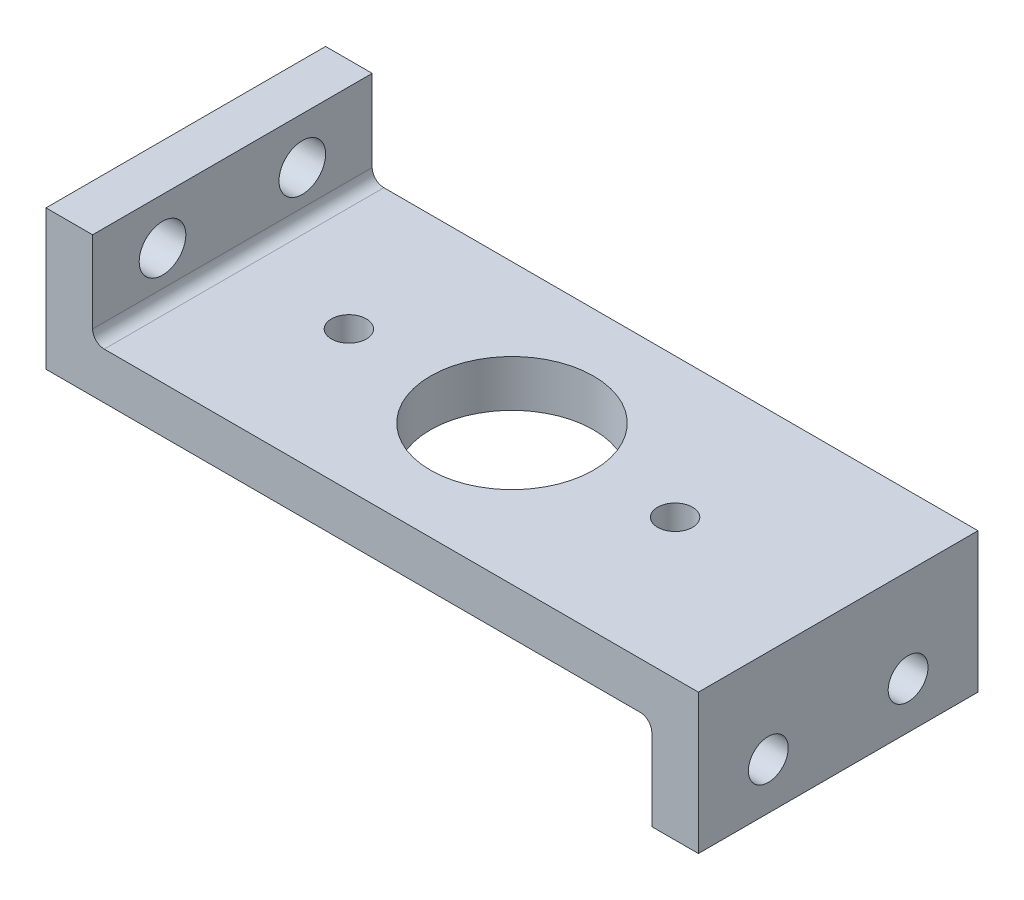
SolidWorks part; units mm, degrees
material "Alloy Steel"
ref_plane "Front Plane" through (0, 0, 0) normal (0, 0, 1) x (1, 0, 0)
ref_plane "Top Plane" through (0, 0, 0) normal (0, 1, 0) x (1, 0, 0)
ref_plane "Right Plane" through (0, 0, 0) normal (1, 0, 0) x (0, 0, -1)
sketch "Sketch1" plane through (0, 0, 0) normal (0, 0, 1) x (1, 0, 0)
  line L1 (-88.9, -4.8927) -> (73.025, -4.8927)
  line L2 (-88.9, -4.8927) -> (-88.9, 4.8927)
  line L3 (-73.025, 7.8073) -> (88.9, 7.8073)
  line L4 (88.9, -4.8927) -> (88.9, 7.8073)
  line L8 (-88.9, 4.8927) -> (-88.9, 33.2073)
  line L9 (-88.9, 33.2073) -> (-76.2, 33.2073)
  line L10 (-76.2, 10.9823) -> (-76.2, 33.2073)
  line L12 (88.9, -4.8927) -> (88.9, -30.2927)
  line L13 (88.9, -30.2927) -> (76.2, -30.2927)
  line L14 (76.2, -8.0677) -> (76.2, -30.2927)
  arc A0 (76.2, -8.0677) -> (73.025, -4.8927) centre (73.025, -8.0677) ccw
  arc A1 (-73.025, 7.8073) -> (-76.2, 10.9823) centre (-73.025, 10.9823) cw
  point P0 (0, 0)
  dimension "D7" = 3.175
  dimension "D1" = 12.7
  dimension "D2" = 12.7
  dimension "D3" = 38.1
  dimension "D4" = 38.1
  dimension "D5" = 177.8
  dimension "D6" = 12.7
extrude "Boss-Extrude1" add sketch "Sketch1" along normal blind 76.2
sketch "Sketch2" plane through (0, 0, 0) normal (0, 1, 0) x (1, 0, 0)
  line L0 (88.9, -76.2) -> (88.9, 0) construction
  line L1 (-34.925, 0) -> (34.925, 0) construction
  line L2 (-108.2905, -38.1) -> (131.2203, -38.1) construction
  line L3 (0, -38.1) -> (0, 39.7458) construction
  line L4 (88.9, -76.2) -> (-73.025, -76.2) construction
  circle A0 centre (0, -38.1) radius 22.225
  circle A1 centre (-44.45, -38.1) radius 4.7625
  circle A2 centre (44.45, -38.1) radius 4.7625
  dimension "D1" = 88.9
  dimension "D3" = 9.525
  dimension "D4" = 44.45
  dimension "D2" = 38.1
  dimension "D5" = 38.1
extrude "Cut-Extrude2" cut sketch "Sketch2" against normal through all both and the other way through all
sketch "Sketch3" plane through (-88.9, 0, 0) normal (-1, 0, 0) x (0, 0, 1)
  line L0 (76.2, 33.2073) -> (0, 33.2073) construction
  line L1 (76.2, 33.2073) -> (76.2, -4.8927) construction
  circle A0 centre (19.05, 20.5073) radius 6.35
  circle A1 centre (57.15, 20.5073) radius 6.35
  dimension "D1" = 12.7
  dimension "D2" = 38.1
  dimension "D4" = 19.05
  dimension "D5" = 12.7
  dimension "D3" = 12.7
extrude "Cut-Extrude3" cut sketch "Sketch3" against normal up to next
sketch "Sketch5" plane through (88.9, 0, 0) normal (1, 0, 0) x (0, 0, -1)
  line L0 (-76.2, -30.2927) -> (0, -30.2927) construction
  line L1 (-76.2, -30.2927) -> (-76.2, 7.8073) construction
  circle A0 centre (-57.15, -17.5927) radius 5.4284
  circle A1 centre (-19.05, -17.5927) radius 5.4284
  dimension "D3" = 38.1
  dimension "D4" = 19.05
  dimension "D1" = 12.7
  dimension "D2" = 12.7
extrude "Cut-Extrude4" cut sketch "Sketch5" against normal blind 76.2
